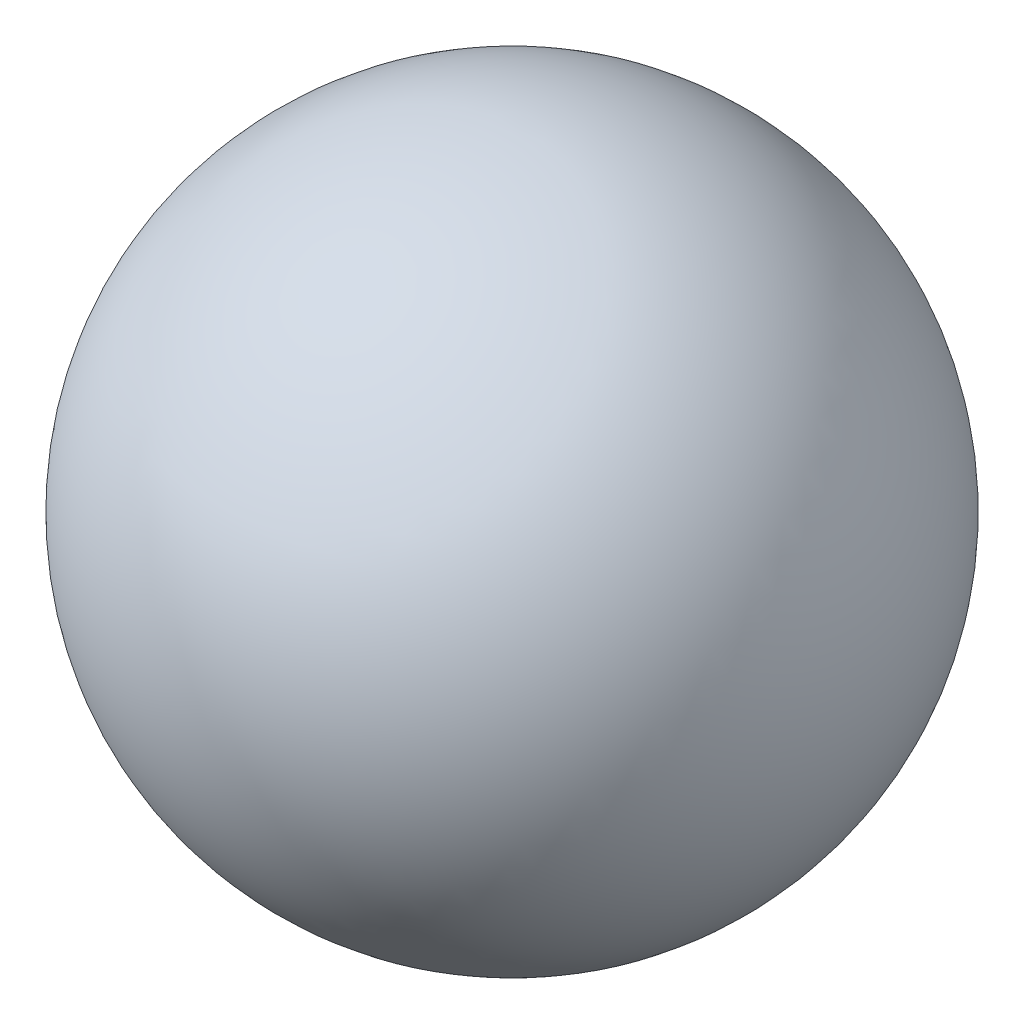
SolidWorks part; units mm, degrees
material "Chrome Stainless Steel"
ref_plane "Front Plane" through (0, 0, 0) normal (0, 0, 1) x (1, 0, 0)
ref_plane "Top Plane" through (0, 0, 0) normal (0, 1, 0) x (1, 0, 0)
ref_plane "Right Plane" through (0, 0, 0) normal (1, 0, 0) x (0, 0, -1)
sketch "Sketch1" plane through (0, 0, 0) normal (0, 0, 1) x (1, 0, 0)
  line L0 (0, 1.19) -> (0, -1.19) construction
  line L1 (0, -1.19) -> (0, 1.19)
  arc A0 (0, -1.19) -> (0, 1.19) centre (0, 0) ccw
  point P4 (0, 0)
revolve "Revolve1" add sketch "Sketch1" angle 360 about L0
